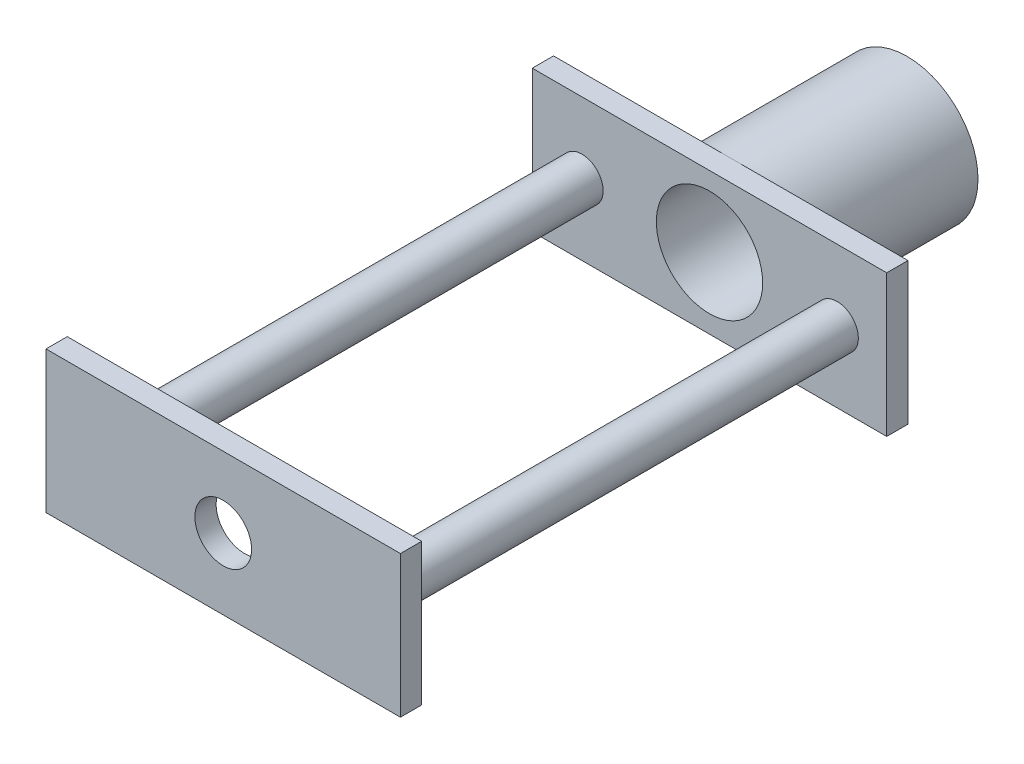
SolidWorks part; units mm, degrees
ref_plane "Front Plane" through (0, 0, 0) normal (0, 0, 1) x (1, 0, 0)
ref_plane "Top Plane" through (0, 0, 0) normal (0, 1, 0) x (1, 0, 0)
ref_plane "Right Plane" through (0, 0, 0) normal (1, 0, 0) x (0, 0, -1)
sketch "Sketch7" plane through (0, 0, 0) normal (0, 0, 1) x (1, 0, 0)
  circle A0 centre (15.5728, -20.5278) radius 50
  dimension "D1" = 100
extrude "Boss-Extrude3" add sketch "Sketch7" along normal blind 124.4
sketch "Sketch8" plane through (0, 0, 124.4) normal (0, 0, 1) x (1, 0, 0)
  circle A0 centre (15.5728, -20.5278) radius 37.5
  circle A1 centre (15.5728, -20.5278) radius 50 construction
  dimension "D2" = 75
  dimension "D1" = 0
extrude "Cut-Extrude3" cut sketch "Sketch8" against normal blind 56 contours A0
sketch "Sketch9" plane through (0, 0, 0) normal (0, 0, -1) x (-1, 0, 0)
  circle A0 centre (-15.5728, -20.5278) radius 32.5
  circle A1 centre (-15.5728, -20.5278) radius 50 construction
  dimension "D2" = 65
  dimension "D1" = 0
extrude "Cut-Extrude4" cut sketch "Sketch9" against normal blind 69.4
sketch "Sketch10" plane through (0, 0, 124.4) normal (0, 0, 1) x (1, 0, 0)
  line L1 (-109.4272, 29.4722) -> (140.5728, 29.4722)
  line L2 (-109.4272, 29.4722) -> (-109.4272, -70.5278)
  line L3 (-109.4272, -70.5278) -> (140.5728, -70.5278)
  line L4 (140.5728, 29.4722) -> (140.5728, -70.5278)
  circle A1 centre (15.5728, -20.5278) radius 50 construction
  point P6 (-67.7995, 29.4722)
  dimension "D1" = 50
  dimension "D2" = 125
  dimension "D3" = 125
  dimension "D4" = 50
extrude "Boss-Extrude4" add sketch "Sketch10" along normal blind 15
sketch "Sketch11" plane through (0, 0, 139.4) normal (0, 0, 1) x (1, 0, 0)
  line L0 (140.5728, 29.4722) -> (-109.4272, 29.4722) construction
  line L1 (140.5728, -70.5278) -> (140.5728, 29.4722) construction
  circle A0 centre (15.5728, -20.5278) radius 37.5
  point P2 (0, 0)
  dimension "D1" = 75
  dimension "D2" = 50
  dimension "D3" = 125
extrude "Cut-Extrude5" cut sketch "Sketch11" against normal blind 15
sketch "Sketch12" plane through (0, 0, 139.4) normal (0, 0, 1) x (1, 0, 0)
  line L0 (-109.4272, -70.5278) -> (140.5728, -70.5278) construction
  line L1 (140.5728, -70.5278) -> (140.5728, 29.4722) construction
  circle A0 centre (105.5728, -20.5278) radius 15
  dimension "D1" = 30
  dimension "D2" = 50
  dimension "D3" = 35
extrude "Boss-Extrude5" add sketch "Sketch12" along normal blind 328
pattern_linear "LPattern1" count 2 spacing 180 along (-1, 0, 0) of "Boss-Extrude5"
sketch "Sketch13" plane through (0, 0, 467.4) normal (0, 0, 1) x (1, 0, 0)
  line L1 (-109.4272, 29.4722) -> (140.5728, 29.4722)
  line L2 (-109.4272, 29.4722) -> (-109.4272, -70.5278)
  line L3 (-109.4272, -70.5278) -> (140.5728, -70.5278)
  line L4 (140.5728, 29.4722) -> (140.5728, -70.5278)
extrude "Boss-Extrude6" add sketch "Sketch13" along normal blind 15
sketch "Sketch15" plane through (0, 0, 482.4) normal (0, 0, 1) x (1, 0, 0)
  line L0 (140.5728, 29.4722) -> (-109.4272, 29.4722) construction
  line L1 (140.5728, -70.5278) -> (140.5728, 29.4722) construction
  circle A0 centre (15.5728, -20.5278) radius 20
  dimension "D3" = 40
  dimension "D1" = 50
  dimension "D2" = 125
extrude "Cut-Extrude6" cut sketch "Sketch15" against normal blind 15
